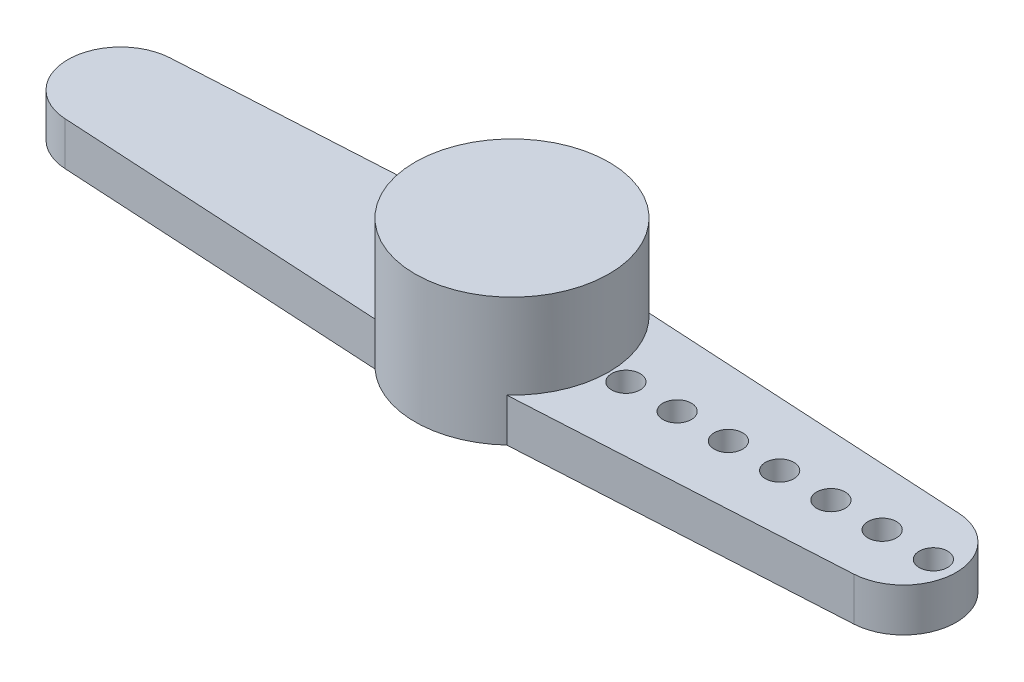
SolidWorks part; units mm, degrees
ref_plane "前视基准面" through (0, 0, 0) normal (0, 0, 1) x (1, 0, 0)
ref_plane "上视基准面" through (0, 0, 0) normal (0, 1, 0) x (1, 0, 0)
ref_plane "右视基准面" through (0, 0, 0) normal (1, 0, 0) x (0, 0, -1)
sketch "草图1" plane through (0, 0, 0) normal (0, 1, 0) x (1, 0, 0)
  circle A0 centre (0, 0) radius 3.405
  dimension "D1" = 6.81
extrude "凸台-拉伸1" add sketch "草图1" along normal blind 4.5
sketch "草图2" plane through (0, 0, 0) normal (0, -1, 0) x (1, 0, 0)
  line L0 (0, 0) -> (15.6, 0) construction
  line L1 (0, 6.9217) -> (0, 0) construction
  line L2 (2.3143, 2.4976) -> (13.8541, 1.8471)
  line L3 (2.3143, -2.4976) -> (13.8541, -1.8471)
  line L4 (-2.3143, -2.4976) -> (-13.8541, -1.8471)
  line L5 (-2.3143, 2.4976) -> (-13.8541, 1.8471)
  arc A0 (13.8541, -1.8471) -> (13.8541, 1.8471) centre (13.75, 0) ccw
  circle A1 centre (0, 0) radius 3.405
  arc A2 (2.3143, 2.4976) -> (-2.3143, 2.4976) centre (0, 0) ccw
  arc A3 (-13.8541, -1.8471) -> (-13.8541, 1.8471) centre (-13.75, 0) cw
  arc A4 (-2.3143, -2.4976) -> (2.3143, -2.4976) centre (0, 0) ccw
  dimension "D3" = 3.7
  dimension "D2" = 15.6
  dimension "D1" = 0
extrude "凸台-拉伸2" add sketch "草图2" against normal blind 1.52
sketch "草图3" plane through (0, 0, 0) normal (0, -1, 0) x (1, 0, 0)
  circle A0 centre (4, 0) radius 0.5
  circle A1 centre (5.8, 0) radius 0.5
  circle A2 centre (7.6, 0) radius 0.5
  circle A3 centre (9.4, 0) radius 0.5
  circle A4 centre (11.2, 0) radius 0.5
  circle A5 centre (13, 0) radius 0.5
  circle A6 centre (14.8, 0) radius 0.5
  dimension "D1" = 1
  dimension "D3" = 4
  dimension "D2" = 7
extrude "切除-拉伸1" cut sketch "草图3" against normal blind 1.52
